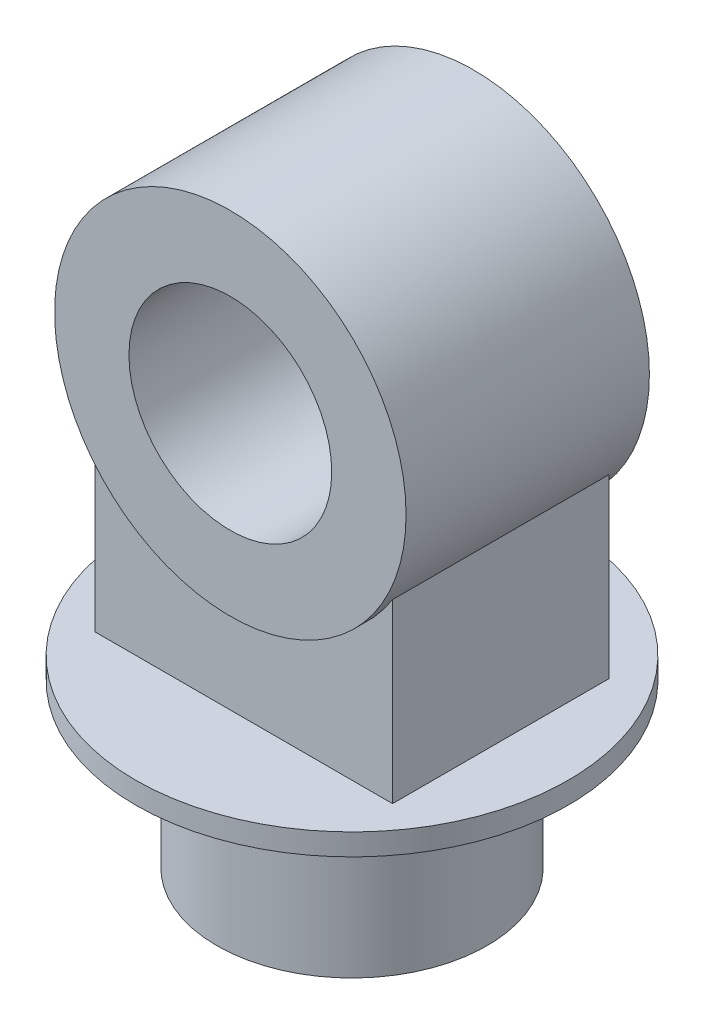
SolidWorks part; units mm, degrees
ref_plane "Front Plane" through (0, 0, 0) normal (0, 0, 1) x (1, 0, 0)
ref_plane "Top Plane" through (0, 0, 0) normal (0, 1, 0) x (1, 0, 0)
ref_plane "Right Plane" through (0, 0, 0) normal (1, 0, 0) x (0, 0, -1)
sketch "Sketch1" plane through (0, 0, 0) normal (0, 1, 0) x (1, 0, 0)
  circle A0 centre (0, 0) radius 100
  dimension "D1" = 200
extrude "Boss-Extrude1" add sketch "Sketch1" along normal blind 120
sketch "Sketch2" plane through (0, 120, 0) normal (0, 1, 0) x (1, 0, 0)
  circle A0 centre (0, 0) radius 160
  dimension "D1" = 320
extrude "Boss-Extrude2" add sketch "Sketch2" along normal blind 16
sketch "Sketch3" plane through (0, 0, 0) normal (0, 0, 1) x (1, 0, 0)
  line L0 (160, 136) -> (-160, 136) construction
  circle A0 centre (0, 336) radius 130
  circle A1 centre (0, 336) radius 75
  dimension "D1" = 150
  dimension "D2" = 260
  dimension "D3" = 200
extrude "Boss-Extrude3" add sketch "Sketch3" along normal mid plane 180 separate body
sketch "Sketch4" plane through (0, 136, 0) normal (0, 1, 0) x (1, 0, 0)
  line L1 (-110, -80) -> (110, -80)
  line L2 (-110, -80) -> (-110, 80)
  line L3 (-110, 80) -> (110, 80)
  line L4 (110, -80) -> (110, 80)
  line L5 (-110, -80) -> (110, 80) construction
  line L6 (-110, 80) -> (110, -80) construction
  point P0 (0, 0)
  dimension "D1" = 160
  dimension "D2" = 220
extrude "Boss-Extrude4" add sketch "Sketch4" along normal up to next
